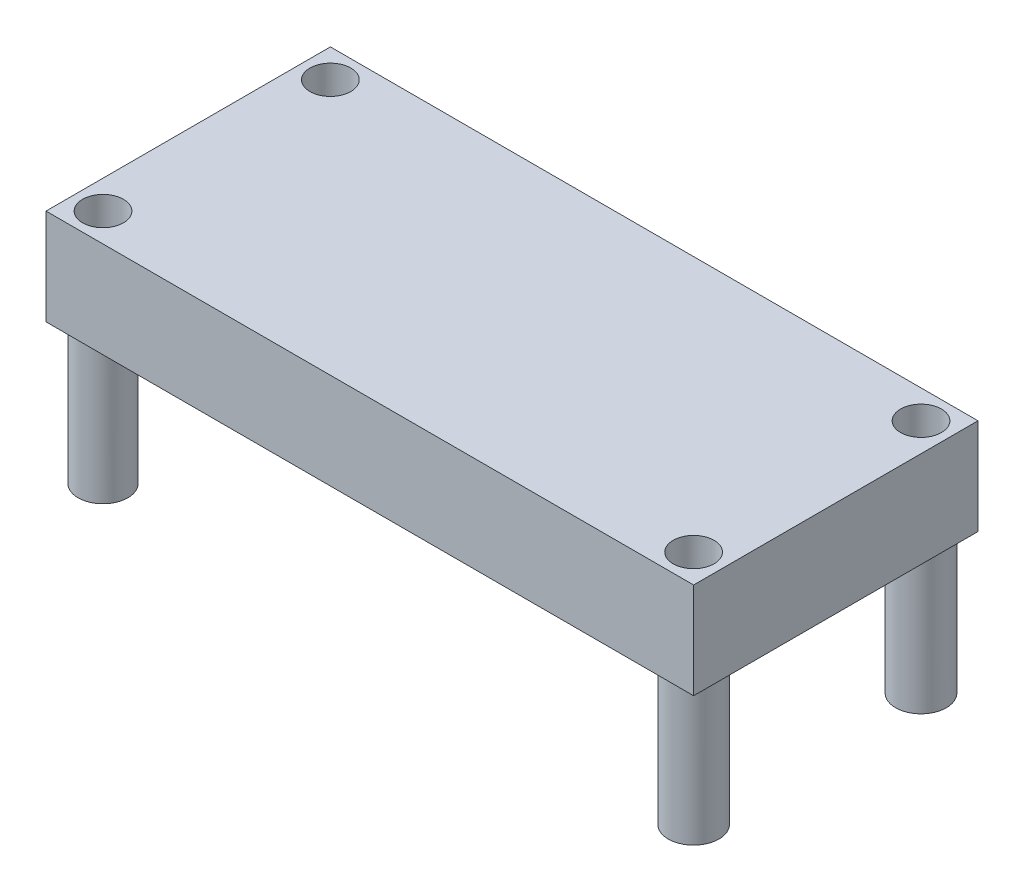
SolidWorks part; units mm, degrees
ref_plane "Front Plane" through (0, 0, 0) normal (0, 0, 1) x (1, 0, 0)
ref_plane "Top Plane" through (0, 0, 0) normal (0, 1, 0) x (1, 0, 0)
ref_plane "Right Plane" through (0, 0, 0) normal (1, 0, 0) x (0, 0, -1)
sketch "Sketch1" plane through (0, 0, 0) normal (0, 1, 0) x (1, 0, 0)
  line L1 (-16.8639, 11.4761) -> (35.0791, 11.4761)
  line L2 (-16.8639, 11.4761) -> (-16.8639, -11.3331)
  line L3 (-16.8639, -11.3331) -> (35.0791, -11.3331)
  line L4 (35.0791, 11.4761) -> (35.0791, -11.3331)
  dimension "D1" = 22.8092
  dimension "D2" = 51.943
extrude "Boss-Extrude1" add sketch "Sketch1" along normal blind 7.6962
sketch "Sketch2" plane through (0, 0, 0) normal (0, -1, 0) x (1, 0, 0)
  line L0 (-16.8639, -11.4761) -> (-16.8639, 11.3331) construction
  line L1 (-16.8639, 11.3331) -> (35.0791, 11.3331) construction
  line L2 (35.0791, -11.4761) -> (-16.8639, -11.4761) construction
  line L3 (35.0791, 11.3331) -> (35.0791, -11.4761) construction
  circle A0 centre (-14.5779, 9.0471) radius 1.9939
  circle A1 centre (32.7931, 9.0471) radius 2.032
  circle A2 centre (32.7931, -9.1901) radius 2.032
  circle A3 centre (-14.5779, -9.1901) radius 2.032
  dimension "D1" = 3.9878
  dimension "D3" = 2.286
  dimension "D6" = 4.064
  dimension "D7" = 2.286
  dimension "D8" = 2.286
  dimension "D9" = 4.064
  dimension "D11" = 2.286
  dimension "D12" = 4.064
  dimension "D2" = 2.286
  dimension "D4" = 2.286
  dimension "D5" = 2.286
  dimension "D10" = 2.286
extrude "Boss-Extrude2" add sketch "Sketch2" along normal blind 11.2268
sketch "Sketch3" plane through (0, -11.2268, 0) normal (0, -1, 0) x (1, 0, 0)
  circle A0 centre (-14.5779, 9.0471) radius 1.6383
  circle A1 centre (-14.5779, -9.1901) radius 1.6383
  circle A2 centre (32.7931, -9.1901) radius 1.6383
  circle A3 centre (32.7931, 9.0471) radius 1.6383
  dimension "D1" = 3.2766
  dimension "D2" = 3.2766
  dimension "D3" = 3.2766
  dimension "D4" = 3.2766
extrude "Cut-Extrude1" cut sketch "Sketch3" against normal through all
